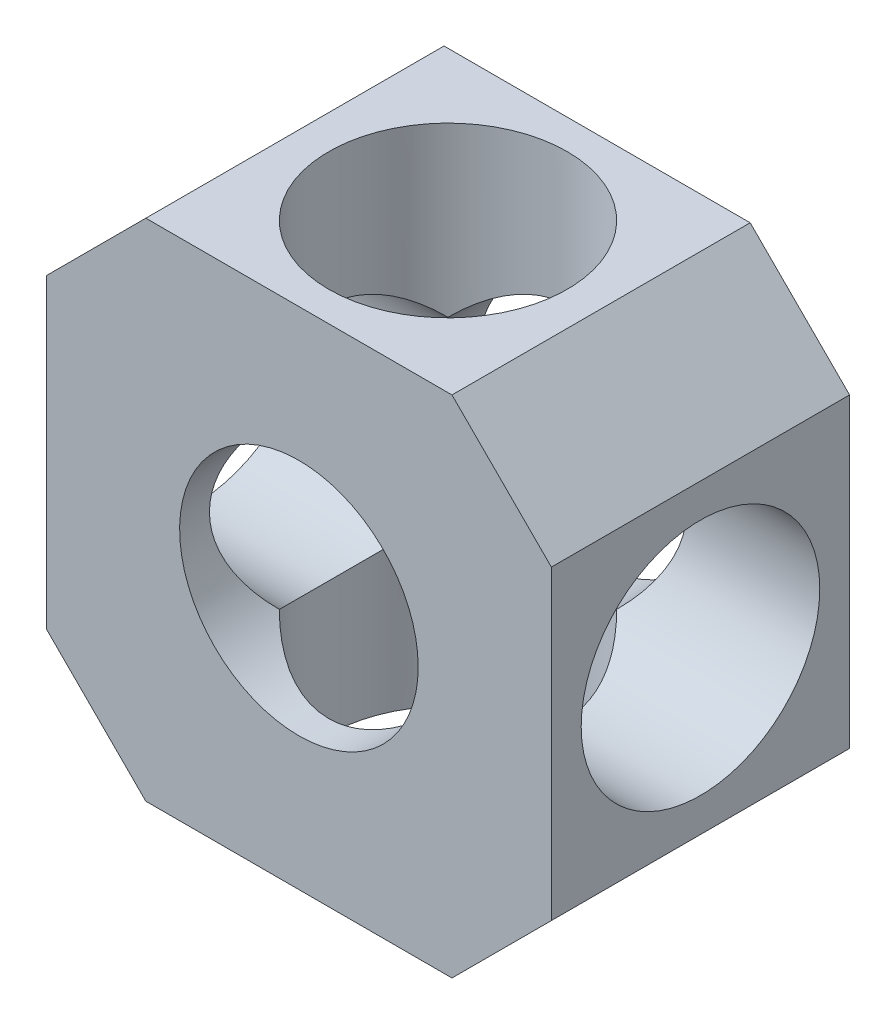
SolidWorks part; units mm, degrees
ref_plane "Front" through (0, 0, 0) normal (0, 0, 1) x (1, 0, 0)
ref_plane "Top" through (0, 0, 0) normal (0, 1, 0) x (1, 0, 0)
ref_plane "Right" through (0, 0, 0) normal (1, 0, 0) x (0, 0, -1)
sketch "Sketch2" plane through (0, 0, 0) normal (0, 0, 1) x (1, 0, 0)
  line L0 (0, 20.4) -> (5, 25.4)
  line L1 (5, 0) -> (20.4, 0)
  line L2 (0, 5) -> (0, 20.4)
  line L3 (5, 25.4) -> (20.4, 25.4)
  line L4 (25.4, 5) -> (25.4, 20.4)
  line L5 (20.4, 25.4) -> (25.4, 20.4)
  line L6 (20.4, 0) -> (25.4, 5)
  line L7 (0, 5) -> (5, 0)
  circle A0 centre (12.7, 12.7) radius 6
  point P0 (0, 0)
  point P1 (25.4, 25.4)
  point P2 (0, 25.4)
  point P3 (25.4, 0)
  dimension "D3" = 12
  dimension "D1" = 25.4
  dimension "D2" = 25.4
  dimension "D4" = 12.7
  dimension "D9" = 12.7
extrude "Boss-Extrude1" add sketch "Sketch2" along normal blind 15
sketch "Sketch3" plane through (25.4, 0, 0) normal (1, 0, 0) x (0, 0, -1)
  line L0 (-15, 5) -> (-15, 20.4) construction
  line L1 (-15, 0) -> (0, 0) construction
  circle A0 centre (-7.5, 12.7) radius 6
  dimension "D3" = 12
  dimension "D1" = 7.5
  dimension "D2" = 12.7
extrude "Cut-Extrude1" cut sketch "Sketch3" against normal blind 27
sketch "Sketch4" plane through (0, 25.4, 0) normal (0, 1, 0) x (1, 0, 0)
  line L0 (20.4, -15) -> (5, -15) construction
  line L1 (0, -15) -> (0, 0) construction
  circle A0 centre (12.7, -7.5) radius 6
  dimension "D1" = 12
  dimension "D2" = 7.5
  dimension "D3" = 12.7
extrude "Cut-Extrude2" cut sketch "Sketch4" against normal blind 27
